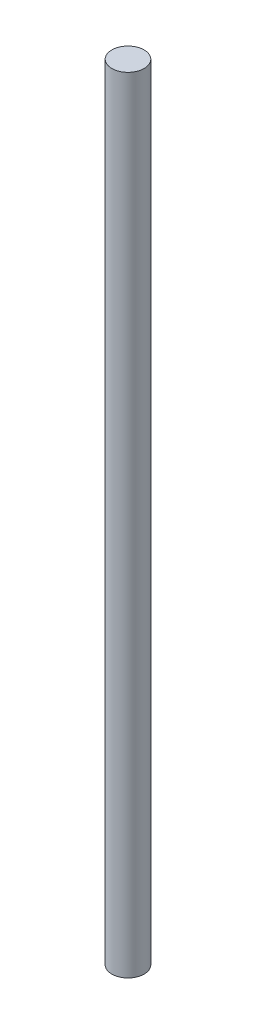
SolidWorks part; units mm, degrees
ref_plane "Front Plane" through (0, 0, 0) normal (0, 0, 1) x (1, 0, 0)
ref_plane "Top Plane" through (0, 0, 0) normal (0, 1, 0) x (1, 0, 0)
ref_plane "Right Plane" through (0, 0, 0) normal (1, 0, 0) x (0, 0, -1)
sketch "Sketch1" plane through (0, 0, 0) normal (0, 1, 0) x (1, 0, 0)
  circle A0 centre (0, 0) radius 2.675
  dimension "D1" = 5.35
extrude "Boss-Extrude1" add sketch "Sketch1" along normal blind 130
